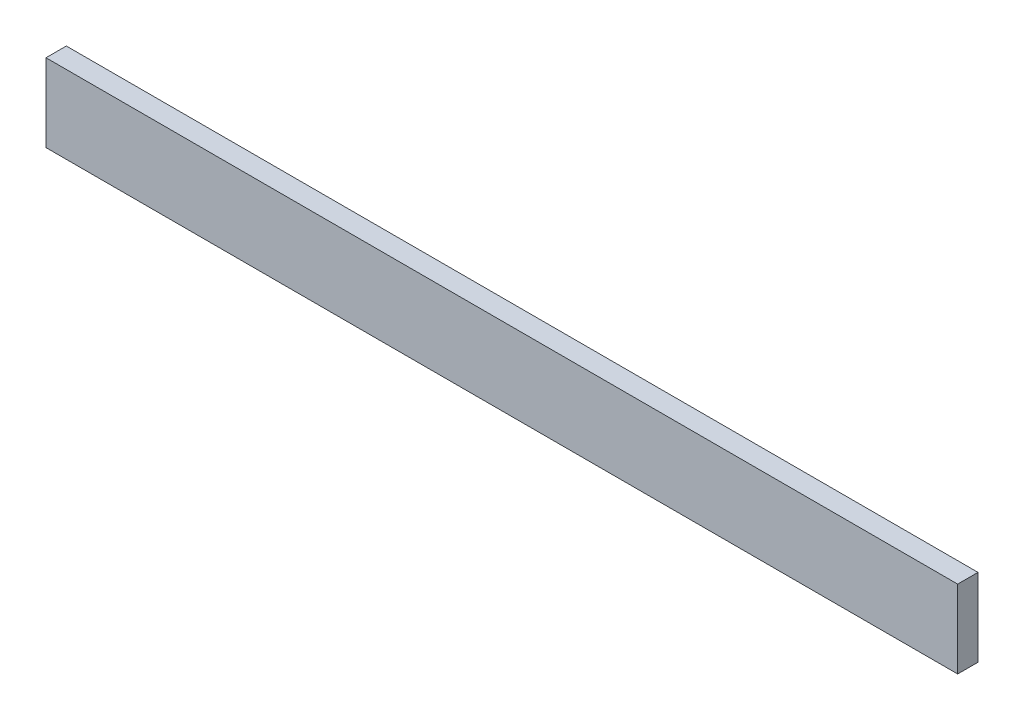
SolidWorks part; units mm, degrees
ref_plane "Front Plane" through (0, 0, 0) normal (0, 0, 1) x (1, 0, 0)
ref_plane "Top Plane" through (0, 0, 0) normal (0, 1, 0) x (1, 0, 0)
ref_plane "Right Plane" through (0, 0, 0) normal (1, 0, 0) x (0, 0, -1)
sketch "Sketch1" plane through (0, 0, 0) normal (0, 0, 1) x (1, 0, 0)
  line L0 (0, 0) -> (448.4172, 0)
  line L1 (448.4172, 0) -> (448.4172, 38.2926)
  line L2 (448.4172, 38.2926) -> (0, 38.2926)
  line L3 (0, 38.2926) -> (0, 0)
extrude "Boss-Extrude1" add sketch "Sketch1" along normal blind 10
